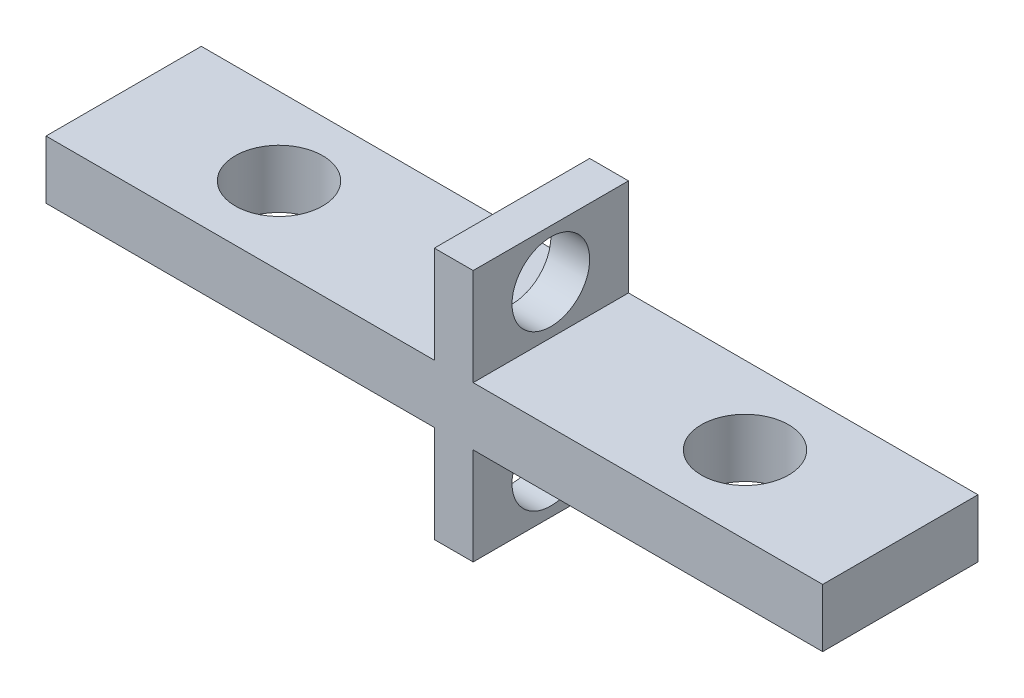
SolidWorks part; units mm, degrees
ref_plane "Front Plane" through (0, 0, 0) normal (0, 0, 1) x (1, 0, 0)
ref_plane "Top Plane" through (0, 0, 0) normal (0, 1, 0) x (1, 0, 0)
ref_plane "Right Plane" through (0, 0, 0) normal (1, 0, 0) x (0, 0, -1)
sketch "Sketch1" plane through (0, 0, 0) normal (0, 1, 0) x (1, 0, 0)
  line L1 (-7.2264, 4.3136) -> (32.7736, 4.3136)
  line L2 (-7.2264, 4.3136) -> (-7.2264, -3.6864)
  line L3 (-7.2264, -3.6864) -> (32.7736, -3.6864)
  line L4 (32.7736, 4.3136) -> (32.7736, -3.6864)
  dimension "D1" = 8
  dimension "D2" = 40
extrude "Boss-Extrude1" add sketch "Sketch1" along normal blind 3
hole_wizard "#8 Clearance Hole1" positions "3DSketch1" profile "Sketch2" hole size "#8" standard "ANSI Inch"
sketch3d "3DSketch1"
  line L0 (-7.2264, 3, -4.3136) -> (-7.2264, 3, 3.6864) construction
  line L1 (32.7736, 3, 3.6864) -> (32.7736, 3, -4.3136) construction
  line L2 (-7.2264, 3, 3.6864) -> (32.7736, 3, 3.6864) construction
  point P0 (0.7736, 3, -0.3136)
  point P2 (24.7736, 3, -0.3136)
  dimension "D1" = 8
  dimension "D2" = 8
  dimension "D3" = 4
  dimension "D4" = 4
  dimension "D5" = 24
sketch "Sketch2" plane through (0.7736, 3, -0.3136) normal (1, 0, 0) x (0, 0, 1)
  line L0 (0, 0) -> (0, 18.3507)
  line L1 (0, 18.3507) -> (2.2479, 17)
  line L2 (2.2479, 17) -> (2.2479, 0)
  line L5 (2.2479, 0) -> (0, 0)
  line L10 (0, 18.3507) -> (-2.2479, 17) construction
  line L11 (0, -6.35) -> (0, 107.95) construction
  dimension "Hole Dia." = 4.4958
  dimension "Hole Depth" = 17
  dimension "Drill Angle" = 118
sketch "Sketch5" plane through (0, 3, 0) normal (0, 1, 0) x (1, 0, 0)
  line L0 (-7.2264, -3.6864) -> (32.7736, -3.6864) construction
  line L1 (12.7736, -3.6864) -> (14.7736, -3.6864)
  line L2 (12.7736, -3.6864) -> (12.7736, 4.3136)
  line L3 (12.7736, 4.3136) -> (14.7736, 4.3136)
  line L4 (14.7736, -3.6864) -> (14.7736, 4.3136)
  line L5 (32.7736, 4.3136) -> (-7.2264, 4.3136) construction
  line L6 (-7.2264, 4.3136) -> (-7.2264, -3.6864) construction
  dimension "D1" = 20
  dimension "D2" = 18
extrude "Boss-Extrude2" add sketch "Sketch5" along normal blind 5 and the other way blind 8
sketch "Sketch6" plane through (12.7736, 0, 0) normal (-1, 0, 0) x (0, 0, 1)
  line L2 (-4.3136, 3) -> (-4.3136, 8) construction
  line L3 (-4.3136, -5) -> (-4.3136, 0) construction
  line L4 (-4.3136, 8) -> (3.6864, 8) construction
  line L5 (-4.3136, -5) -> (3.6864, -5) construction
  circle A0 centre (-0.3136, 5.5) radius 2
  circle A1 centre (-0.3136, -2.5) radius 2
  dimension "D1" = 4
  dimension "D2" = 4
  dimension "D3" = 2.5
  dimension "D4" = 2.5
extrude "Cut-Extrude1" cut sketch "Sketch6" against normal blind 2
